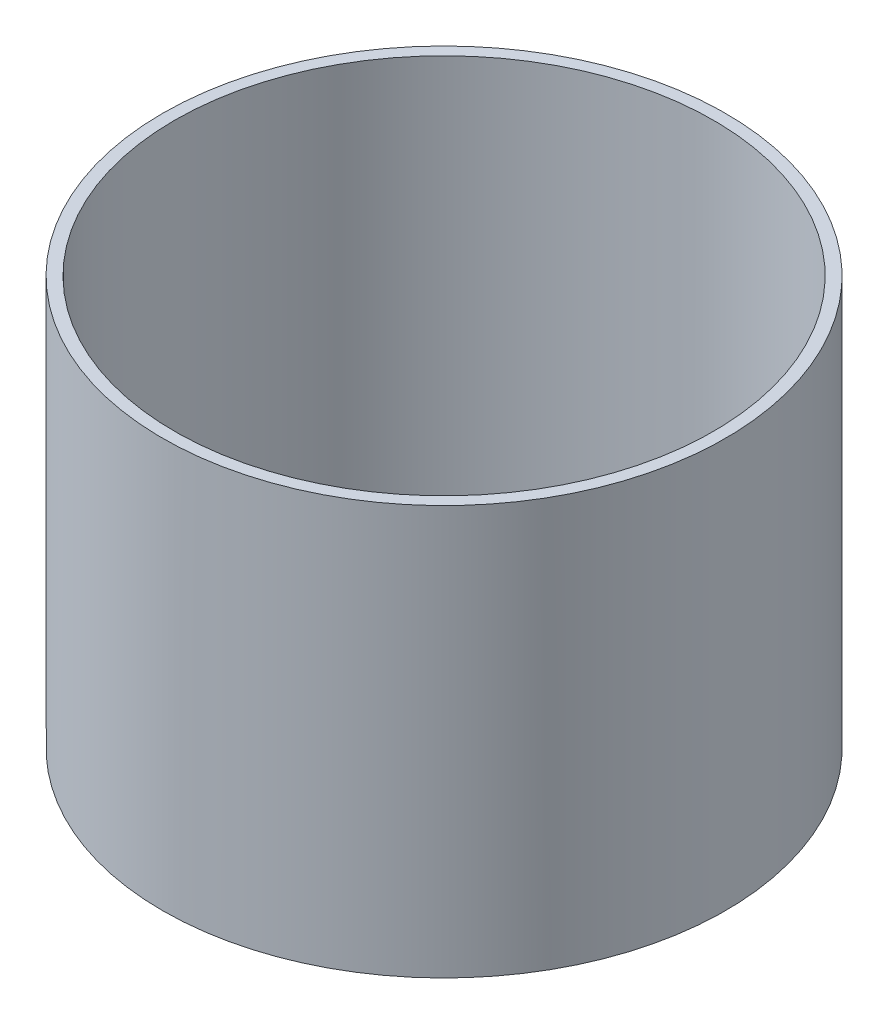
SolidWorks part; units mm, degrees
ref_plane "Front Plane" through (0, 0, 0) normal (0, 0, 1) x (1, 0, 0)
ref_plane "Top Plane" through (0, 0, 0) normal (0, 1, 0) x (1, 0, 0)
ref_plane "Right Plane" through (0, 0, 0) normal (1, 0, 0) x (0, 0, -1)
sketch "Sketch1" plane through (0, 0, 0) normal (0, 1, 0) x (1, 0, 0)
  circle A0 centre (0, 0) radius 57.15
  circle A1 centre (0, 0) radius 59.69
  dimension "D2" = 114.3
  dimension "D1" = 2.54
extrude "Boss-Extrude1" add sketch "Sketch1" along normal up to surface (86.7672 mm away)
ref_plane "Plane1" through (0, 0, 59.69) normal (0, 0, 1) x (1, 0, 0)
equation "\"Foamcore\"= 0.2in"
equation "\"MDF\"= 0.2in"
